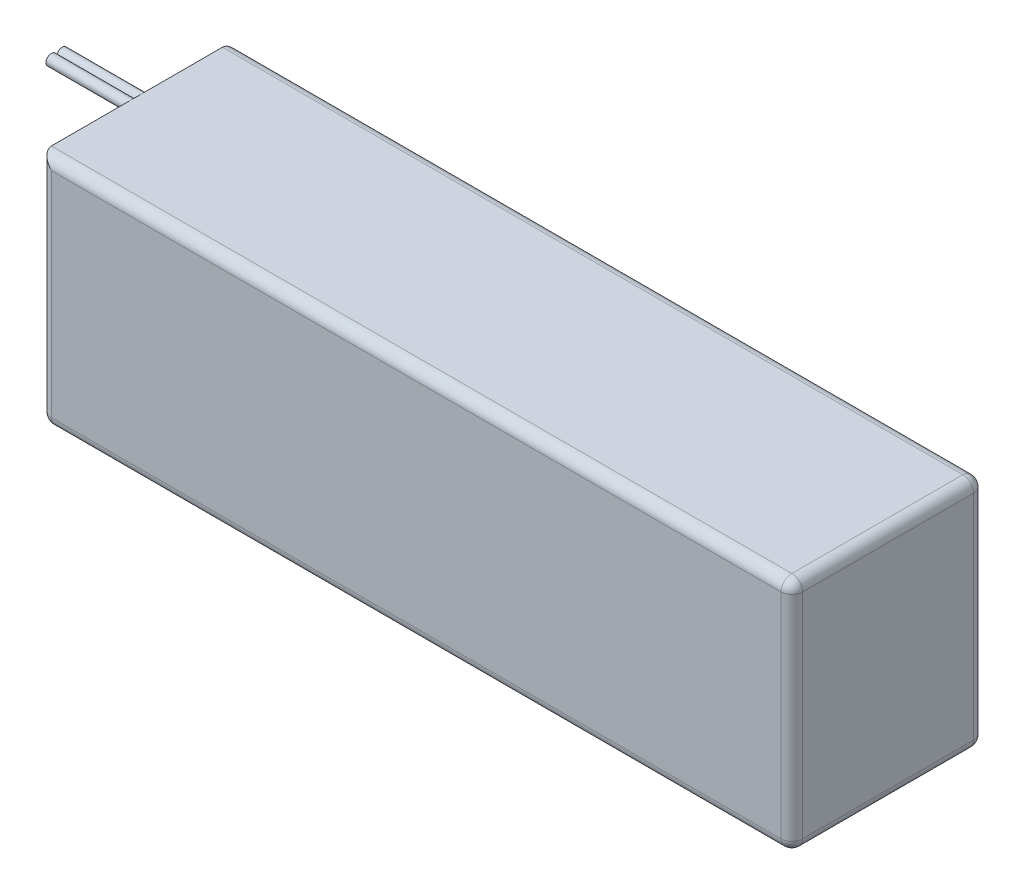
SolidWorks part; units mm, degrees
ref_plane "Front Plane" through (0, 0, 0) normal (0, 0, 1) x (1, 0, 0)
ref_plane "Top Plane" through (0, 0, 0) normal (0, 1, 0) x (1, 0, 0)
ref_plane "Right Plane" through (0, 0, 0) normal (1, 0, 0) x (0, 0, -1)
sketch "Sketch1" plane through (0, 0, 0) normal (0, 0, 1) x (1, 0, 0)
  line L1 (-70.25, -22) -> (70.25, -22)
  line L2 (-70.25, -22) -> (-70.25, 22)
  line L3 (-70.25, 22) -> (70.25, 22)
  line L4 (70.25, -22) -> (70.25, 22)
  line L5 (-70.25, -22) -> (70.25, 22) construction
  line L6 (-70.25, 22) -> (70.25, -22) construction
  point P0 (0, 0)
  dimension "D1" = 140.5
  dimension "D2" = 44
extrude "Boss-Extrude1" add sketch "Sketch1" along normal blind 36
sketch "Sketch2" plane through (-70.25, 0, 0) normal (-1, 0, 0) x (0, 0, 1)
  line L0 (36, 22) -> (0, 22) construction
  line L1 (16.995, 21) -> (19.005, 21) construction
  circle A0 centre (16.995, 21) radius 1
  circle A1 centre (19.005, 21) radius 1
  point P8 (18, 22)
  point P9 (18, 21)
  dimension "D1" = 2
  dimension "D2" = 2.01
extrude "Boss-Extrude4" add sketch "Sketch2" along normal blind 15 separate body
fillet "Fillet1" radius 2 11 edges at (-70.25, 0, 0) (-70.25, -22, 18) (0, -22, 0) (70.25, -22, 18) (70.25, 0, 0) (0, -22, 36) (-70.25, 0, 36) (70.25, 0, 36) (70.25, 22, 18) (0, 22, 36) (0, 22, 0)
